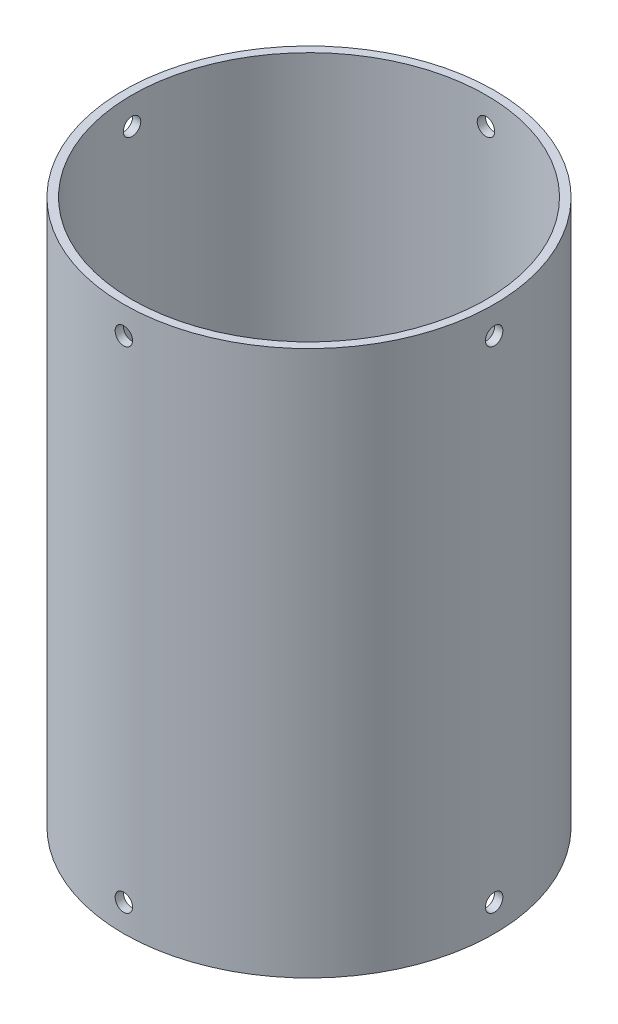
SolidWorks part; units mm, degrees
ref_plane "前视基准面" through (0, 0, 0) normal (0, 0, 1) x (1, 0, 0)
ref_plane "上视基准面" through (0, 0, 0) normal (0, 1, 0) x (1, 0, 0)
ref_plane "右视基准面" through (0, 0, 0) normal (1, 0, 0) x (0, 0, -1)
sketch "草图1" plane through (0, 0, 0) normal (0, 1, 0) x (1, 0, 0)
  circle A0 centre (0, 0) radius 32.5
  circle A1 centre (0, 0) radius 34
  dimension "D1" = 65
  dimension "D2" = 68
extrude "凸台-拉伸1" add sketch "草图1" along normal blind 100
ref_plane "基准面2" through (0, 50, 0) normal (0, 1, 0) x (1, 0, 0)
ref_plane "基准面1" through (0, 0, 34) normal (0, 0, 1) x (1, 0, 0)
sketch "草图3" plane through (0, 0, 34) normal (0, 0, 1) x (1, 0, 0)
  line L0 (-34, 0) -> (34, 0) construction
  circle A0 centre (0, 5) radius 1.6
  dimension "D1" = 3.2
  dimension "D2" = 5
extrude "切除-拉伸4" cut sketch "草图3" against normal up to next
pattern_circular "阵列(圆周)1" count 4 over 360 about axis through (0, 100, 0) along (0, -1, 0) of "切除-拉伸4"
mirror "镜向2" [suppressed] about plane through (0, 50, 0) normal (0, 1, 0)
sketch "草图4" plane through (0, 0, 34) normal (0, 0, 1) x (1, 0, 0)
  line L0 (0, 100) -> (0, 95)
  line L1 (32.5, 100) -> (-32.5, 100) construction
  dimension "D1" = 5
sketch "草图5" plane through (0, 0, 34) normal (0, 0, 1) x (1, 0, 0)
  circle A0 centre (0, 95) radius 1.6
  dimension "D1" = 3.2
extrude "切除-拉伸5" cut sketch "草图5" against normal up to next
pattern_circular "阵列(圆周)2" count 4 over 360 about axis through (0, 100, 0) along (0, -1, 0) of "切除-拉伸5"
sketch "草图7" [suppressed] plane through (0, 0, 34) normal (0, 0, 1) x (1, 0, 0)
  circle A0 centre (0, 25) radius 14
  dimension "D1" = 28
  dimension "D2" = 25
extrude "切除-拉伸6" [suppressed] cut sketch "草图7" against normal through all
